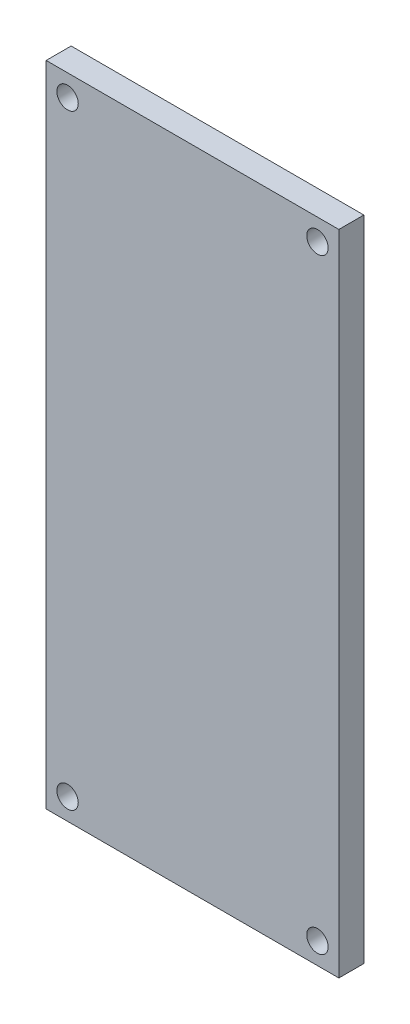
SolidWorks part; units mm, degrees
ref_plane "Front Plane" through (0, 0, 0) normal (0, 0, 1) x (1, 0, 0)
ref_plane "Top Plane" through (0, 0, 0) normal (0, 1, 0) x (1, 0, 0)
ref_plane "Right Plane" through (0, 0, 0) normal (1, 0, 0) x (0, 0, -1)
sketch "Sketch1" plane through (0, 0, 0) normal (0, 0, 1) x (1, 0, 0)
  line L0 (10.25, 0) -> (-10.25, 0) construction
  line L1 (-10.25, 22.7) -> (10.25, 22.7)
  line L2 (-10.25, 22.7) -> (-10.25, -22.7)
  line L3 (-10.25, -22.7) -> (10.25, -22.7)
  line L4 (10.25, 22.7) -> (10.25, -22.7)
  dimension "D1" = 20.5
  dimension "D2" = 45.4
extrude "Extrude1" add sketch "Sketch1" along normal blind 1.75
sketch "Sketch2" plane through (0, 0, 1.75) normal (0, 0, 1) x (1, 0, 0)
  line L0 (-10.25, -22.7) -> (10.25, -22.7) construction
  line L3 (10.25, -22.7) -> (10.25, 22.7) construction
  circle A0 centre (8.75, -21.2) radius 0.75
  dimension "D1" = 1.5
  dimension "D2" = 1.5
  dimension "D3" = 1.5
extrude "Cut-Extrude1" cut sketch "Sketch2" against normal up to surface (1.75 mm away) up to face at (0, 0, 0)
mirror "Mirror1" about plane through (0, 0, 0) normal (1, 0, 0) of "Cut-Extrude1"
mirror "Mirror2" about plane through (0, 0, 0) normal (0, 1, 0) of "Cut-Extrude1", "Mirror1"
